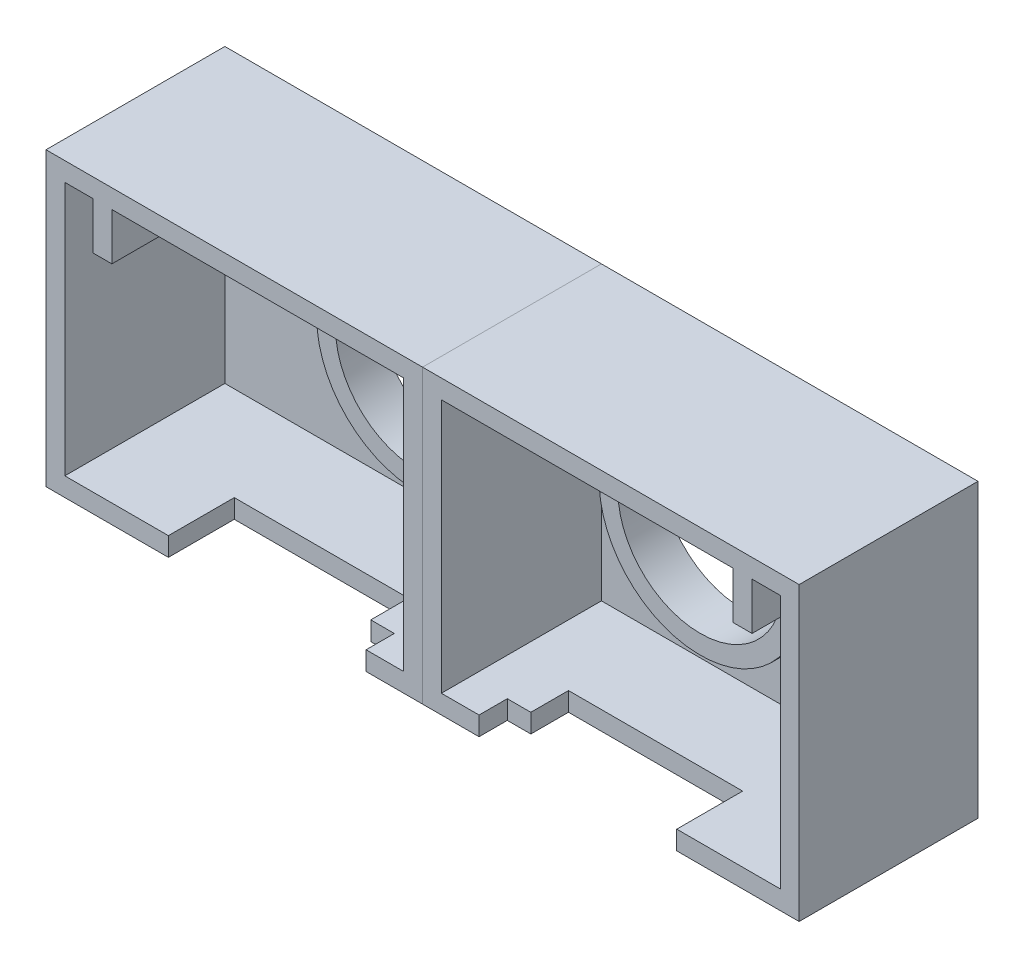
SolidWorks part; units mm, degrees
ref_plane "Front Plane" through (0, 0, 0) normal (0, 0, 1) x (1, 0, 0)
ref_plane "Top Plane" through (0, 0, 0) normal (0, 1, 0) x (1, 0, 0)
ref_plane "Right Plane" through (0, 0, 0) normal (1, 0, 0) x (0, 0, -1)
sketch "Sketch1" plane through (0, 0, 0) normal (0, 0, 1) x (1, 0, 0)
  line L1 (-25, -15.5) -> (15, -15.5)
  line L2 (-25, -15.5) -> (-25, 15.5)
  line L3 (-25, 15.5) -> (15, 15.5)
  line L4 (15, -15.5) -> (15, 15.5)
  circle A0 centre (0, 0) radius 8.75
  point P8 (-25, 0)
  dimension "D1" = 17.5
  dimension "D2" = 40
  dimension "D3" = 31
  dimension "D4" = 25
extrude "Boss-Extrude1" add sketch "Sketch1" against normal blind 19
shell "Shell1" thickness 2
sketch "Sketch2" plane through (0, 0, 0) normal (0, 0, 1) x (1, 0, 0)
  circle A0 centre (0, 0) radius 8.75
  circle A1 centre (0, 0) radius 10.75
  circle A2 centre (0, 0) radius 8.75 construction
  circle A3 centre (0, 0) radius 10.75 construction
extrude "Cut-Extrude1" cut sketch "Sketch2" against normal offset from surface (14.5 mm away) 2.5 up to face at (-10.75, 0, -17)
sketch "Sketch3" plane through (0, 0, -17) normal (0, 0, 1) x (1, 0, 0)
  line L0 (-23, 13.5) -> (-23, -13.5) construction
  line L1 (-20, 13.5) -> (-18, 13.5)
  line L2 (-20, 13.5) -> (-20, 8.5)
  line L3 (-20, 8.5) -> (-18, 8.5)
  line L4 (-18, 13.5) -> (-18, 8.5)
  line L5 (13, 13.5) -> (-23, 13.5) construction
  dimension "D1" = 2
  dimension "D2" = 5
  dimension "D3" = 3
extrude "Boss-Extrude2" add sketch "Sketch3" along normal up to surface (17 mm away) up to face at (-5, 0, 0)
sketch "Sketch8" plane through (0, 0, -17) normal (0, 0, 1) x (1, 0, 0)
  line L0 (13, 13.5) -> (-18, 13.5) construction
  line L1 (-18, 6.5) -> (-11, 6.5)
  line L2 (-18, 6.5) -> (-18, 13.5)
  line L3 (-18, 13.5) -> (-11, 13.5)
  line L4 (-11, 6.5) -> (-11, 13.5)
  line L5 (-18, 8.5) -> (-18, 13.5) construction
  dimension "D1" = 7
  dimension "D2" = 7
extrude "Boss-Extrude3" add sketch "Sketch8" along normal blind 3
hole_wizard "CBORE for M3 SHCS1" positions "Sketch7" profile "Sketch5" counterbore size "M3" standard "ANSI Metric" end condition through all
sketch "Sketch7" plane through (0, 0, -19) normal (0, 0, -1) x (-1, 0, 0)
  line L0 (18, 13.5) -> (18, 8.5) construction
  line L1 (-13, 13.5) -> (18, 13.5) construction
  point P0 (15, 10.5)
  dimension "D1" = 3
  dimension "D2" = 3
sketch "Sketch5" plane through (-15, 10.5, -19) normal (1, 0, 0) x (0, 1, 0)
  line L0 (0, 0) -> (0, 19)
  line L1 (0, 19) -> (1.7, 19)
  line L3 (1.7, 19) -> (1.7, 3)
  line L4 (1.7, 3) -> (3.25, 3)
  line L5 (3.25, 3) -> (3.25, 0)
  line L7 (3.25, 0) -> (0, 0)
  line L11 (0, -6.35) -> (0, 107.95) construction
  dimension "Thru Hole Dia." = 3.4
  dimension "Thru Hole Depth" = 19
  dimension "C'Bore Dia." = 6.5
  dimension "C'Bore Depth" = 3
sketch "Sketch9" plane through (0, -15.5, 0) normal (0, -1, 0) x (1, 0, 0)
  line L0 (-25, 0) -> (15, 0) construction
  line L1 (-12, 0) -> (6.5, 0)
  line L2 (-12, 0) -> (-12, -7)
  line L3 (-12, -7) -> (6.5, -7)
  line L4 (6.5, -3) -> (6.5, -7)
  line L5 (-25, -19) -> (-25, 0) construction
  line L6 (15, -19) -> (15, 0) construction
  line L7 (6.5, -3) -> (9, -3)
  line L8 (9, -3) -> (9, 0)
  line L9 (-25, 0) -> (15, 0) construction
  line L10 (9, 0) -> (6.5, 0)
  dimension "D1" = 18.5
  dimension "D2" = 13
  dimension "D3" = 7
  dimension "D5" = 6
  dimension "D6" = 3
  dimension "D7" = 2.5
extrude "Cut-Extrude3" cut sketch "Sketch9" against normal up to next
mirror "Mirror2" about plane through (15, -15.5, -19) normal (1, 0, 0) of bodies 107
